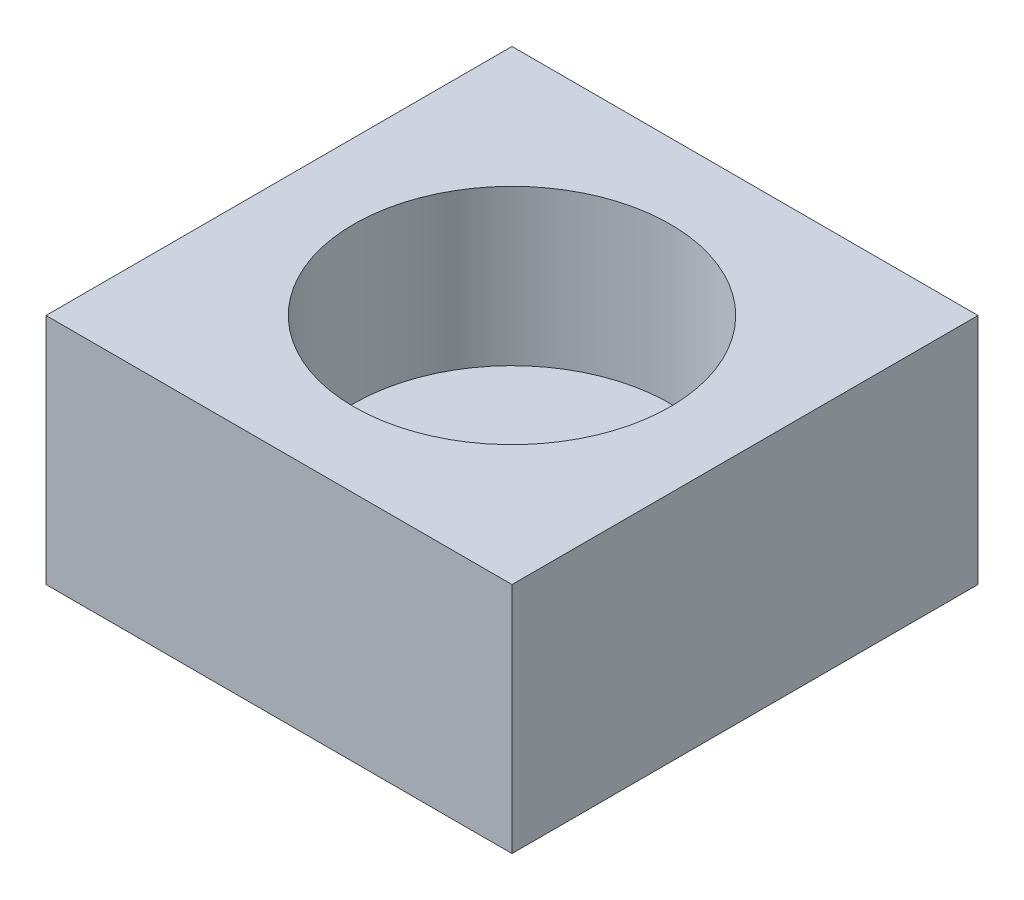
SolidWorks part; units mm, degrees
ref_plane "Plan de face" through (0, 0, 0) normal (0, 0, 1) x (1, 0, 0)
ref_plane "Plan de dessus" through (0, 0, 0) normal (0, 1, 0) x (1, 0, 0)
ref_plane "Plan de droite" through (0, 0, 0) normal (1, 0, 0) x (0, 0, -1)
sketch "Esquisse1" plane through (0, 0, 0) normal (0, 1, 0) x (1, 0, 0)
  line L1 (0, 0) -> (6, 0)
  line L2 (0, 0) -> (0, 6)
  line L3 (0, 6) -> (6, 6)
  line L4 (6, 0) -> (6, 6)
  dimension "D1" = 6
  dimension "D2" = 6
extrude "Extrusion1" add sketch "Esquisse1" along normal blind 3
sketch "Esquisse2" plane through (0, 3, 0) normal (0, 1, 0) x (-1, 0, 0)
  circle A0 centre (-3, -3) radius 2.0371
extrude "Enlèv. mat.-Extru.1" cut sketch "Esquisse2" against normal blind 2
